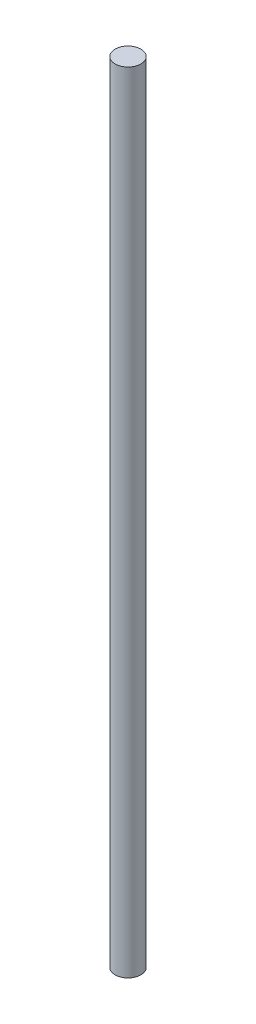
SolidWorks part; units mm, degrees
ref_plane "Plano frontal" through (0, 0, 0) normal (0, 0, 1) x (1, 0, 0)
ref_plane "Plano superior" through (0, 0, 0) normal (0, 1, 0) x (1, 0, 0)
ref_plane "Plano direito" through (0, 0, 0) normal (1, 0, 0) x (0, 0, -1)
sketch "Esboço1" plane through (0, 0, 0) normal (0, 1, 0) x (1, 0, 0)
  circle A0 centre (0, 0) radius 2.45
  dimension "D1" = 4.9
extrude "Ressalto-extrusão1" add sketch "Esboço1" along normal blind 150
